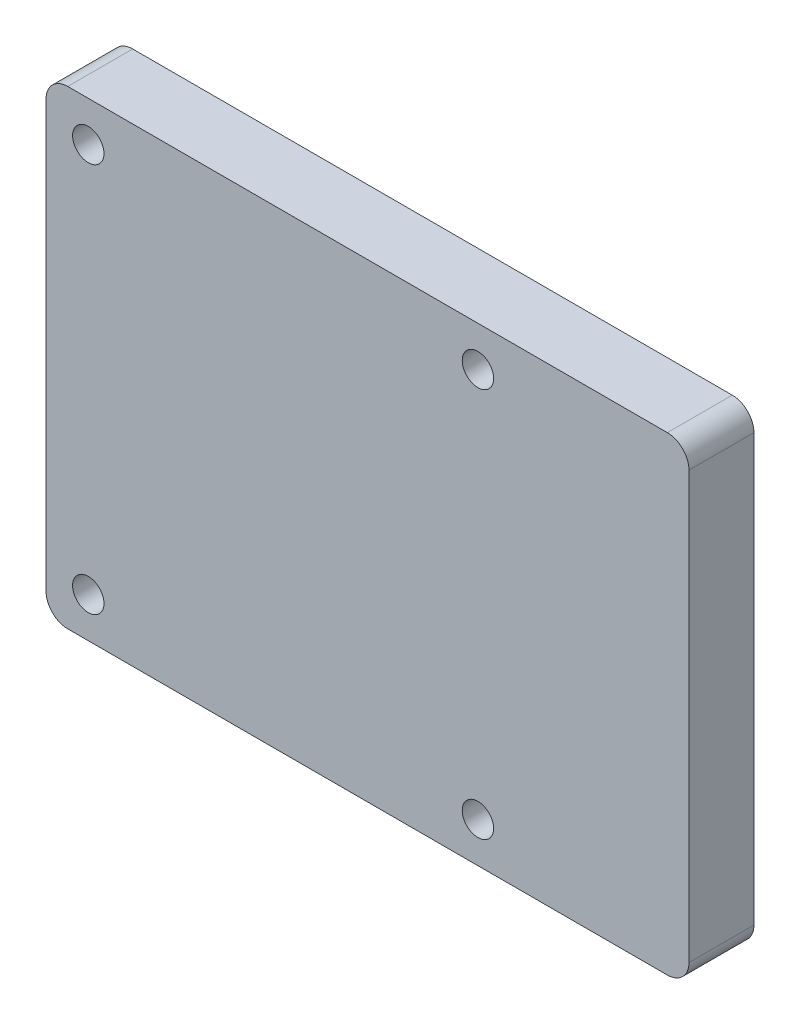
SolidWorks part; units mm, degrees
ref_plane "Front Plane" through (0, 0, 0) normal (0, 0, 1) x (1, 0, 0)
ref_plane "Top Plane" through (0, 0, 0) normal (0, 1, 0) x (1, 0, 0)
ref_plane "Right Plane" through (0, 0, 0) normal (1, 0, 0) x (0, 0, -1)
ref_plane "基准面1" through (0, 0, -6) normal (0, 0, -1) x (-1, 0, 0)
sketch "草图1" plane through (0, 0, -6) normal (0, 0, -1) x (-1, 0, 0)
  line L0 (-29.7, 21.7) -> (-29.7, -21.7)
  line L1 (-29.7, -21.7) -> (29.7, -21.7)
  line L2 (29.7, -21.7) -> (29.7, 21.7)
  line L3 (29.7, 21.7) -> (-29.7, 21.7)
extrude "凸台-拉伸1" add sketch "草图1" against normal blind 6
sketch "草图2" plane through (0, 0, -6) normal (0, 0, -1) x (-1, 0, 0)
  line L0 (-28.2, -20.2) -> (28.2, -20.2)
  line L1 (28.2, -20.2) -> (28.2, 20.2)
  line L2 (28.2, 20.2) -> (-28.2, 20.2)
  line L3 (-28.2, 20.2) -> (-28.2, -20.2)
extrude "切除-拉伸1" cut sketch "草图2" against normal blind 5
sketch "草图3" plane through (0, 0, -1) normal (0, 0, -1) x (-1, 0, 0)
  line L0 (-13.6293, 20.2) -> (-6.7707, 20.2)
  arc A0 (-12.1596, 18.4) -> (-13.6293, 20.2) centre (-13.6293, 18.7) ccw
  arc A1 (-6.7707, 20.2) -> (-8.2404, 18.4) centre (-6.7707, 18.7) ccw
  arc A2 (-8.2404, 18.4) -> (-12.1596, 18.4) centre (-10.2, 18) cw
extrude "凸台-拉伸2" add sketch "草图3" along normal blind 3.2
sketch "草图4" plane through (0, 0, -1) normal (0, 0, -1) x (-1, 0, 0)
  line L0 (22.3707, 20.2) -> (28.2, 20.2)
  line L1 (28.2, 20.2) -> (28.2, 14.6177)
  arc A0 (28.2, 14.6177) -> (26.3143, 16.0673) centre (26.7, 14.6177) ccw
  arc A1 (26.3143, 16.0673) -> (23.8404, 18.4) centre (25.8, 18) cw
  arc A2 (23.8404, 18.4) -> (22.3707, 20.2) centre (22.3707, 18.7) ccw
extrude "凸台-拉伸3" add sketch "草图4" along normal blind 3.2
sketch "草图5" plane through (0, 0, -1) normal (0, 0, -1) x (-1, 0, 0)
  line L0 (28.2, -14.6177) -> (28.2, -20.2)
  line L1 (28.2, -20.2) -> (22.3707, -20.2)
  arc A0 (22.3707, -20.2) -> (23.8404, -18.4) centre (22.3707, -18.7) ccw
  arc A1 (23.8404, -18.4) -> (26.3143, -16.0673) centre (25.8, -18) cw
  arc A2 (26.3143, -16.0673) -> (28.2, -14.6177) centre (26.7, -14.6177) ccw
extrude "凸台-拉伸4" add sketch "草图5" along normal blind 3.2
sketch "草图6" plane through (0, 0, -1) normal (0, 0, -1) x (-1, 0, 0)
  line L0 (-6.7707, -20.2) -> (-13.6293, -20.2)
  arc A0 (-8.2404, -18.4) -> (-6.7707, -20.2) centre (-6.7707, -18.7) ccw
  arc A1 (-13.6293, -20.2) -> (-12.1596, -18.4) centre (-13.6293, -18.7) ccw
  arc A2 (-12.1596, -18.4) -> (-8.2404, -18.4) centre (-10.2, -18) cw
extrude "凸台-拉伸5" add sketch "草图6" along normal blind 3.2
fillet "圆角1" radius 1 4 edges at (-28.2, 20.2, -5.1) (28.2, -20.2, -3.5) (28.2, 20.2, -3.5) (-28.2, -20.2, -5.1)
fillet "圆角2" radius 2 4 edges at (29.7, 21.7, -3) (-29.7, 21.7, -3) (29.7, -21.7, -3) (-29.7, -21.7, -3)
sketch "草图7" plane through (0, 0, -4.2) normal (0, 0, -1) x (-1, 0, 0)
  circle A0 centre (-10.2, 18) radius 1.45
  circle A1 centre (-10.2, -18) radius 1.45
  circle A2 centre (25.8, 18) radius 1.45
  circle A3 centre (25.8, -18) radius 1.45
  dimension "D1" = 2.9
  dimension "D2" = 2.9
  dimension "D3" = 2.9
  dimension "D4" = 2.9
extrude "切除-拉伸2" cut sketch "草图7" against normal blind 20
